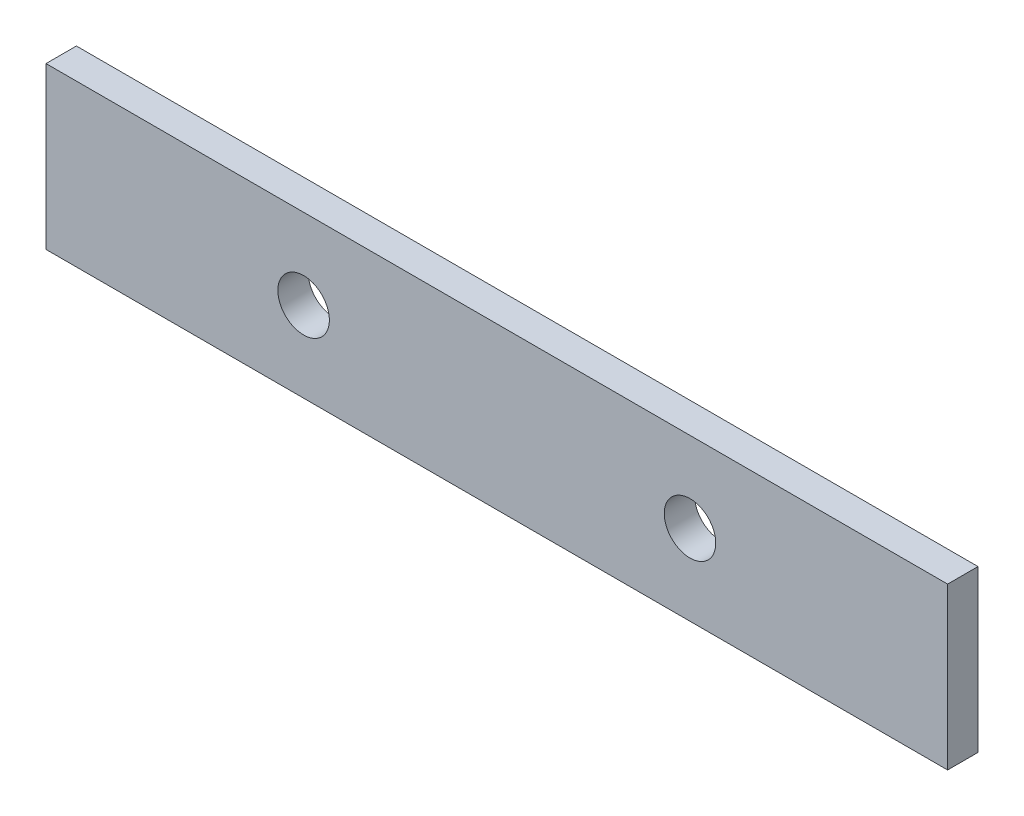
SolidWorks part; units mm, degrees
ref_plane "Front" through (0, 0, 0) normal (0, 0, 1) x (1, 0, 0)
ref_plane "Top" through (0, 0, 0) normal (0, 1, 0) x (1, 0, 0)
ref_plane "Right" through (0, 0, 0) normal (1, 0, 0) x (0, 0, -1)
sketch "Sketch1" plane through (0, 0, 0) normal (0, 0, 1) x (1, 0, 0)
  line L1 (-44.45, -7.9375) -> (44.45, -7.9375)
  line L2 (-44.45, -7.9375) -> (-44.45, 7.9375)
  line L3 (-44.45, 7.9375) -> (44.45, 7.9375)
  line L4 (44.45, -7.9375) -> (44.45, 7.9375)
  line L5 (-44.45, -7.9375) -> (44.45, 7.9375) construction
  line L6 (-44.45, 7.9375) -> (44.45, -7.9375) construction
  point P0 (0, 0)
  dimension "D1" = 88.9
  dimension "D2" = 15.875
extrude "Boss-Extrude1" add sketch "Sketch1" along normal mid plane 2.9972
sketch "Sketch2" plane through (0, 0, -1.4986) normal (0, 0, -1) x (-1, 0, 0)
  line L0 (0, 7.9375) -> (0, -7.9375) construction
  line L1 (-44.45, 7.9375) -> (44.45, 7.9375) construction
  line L2 (44.45, -7.9375) -> (-44.45, -7.9375) construction
  line L3 (19.05, 0) -> (0, 0) construction
  circle A0 centre (-19.05, 0) radius 2.54
  circle A1 centre (19.05, 0) radius 2.54
  dimension "D1" = 38.1
  dimension "D2" = 5.08
extrude "Cut-Extrude1" cut sketch "Sketch2" against normal through all
